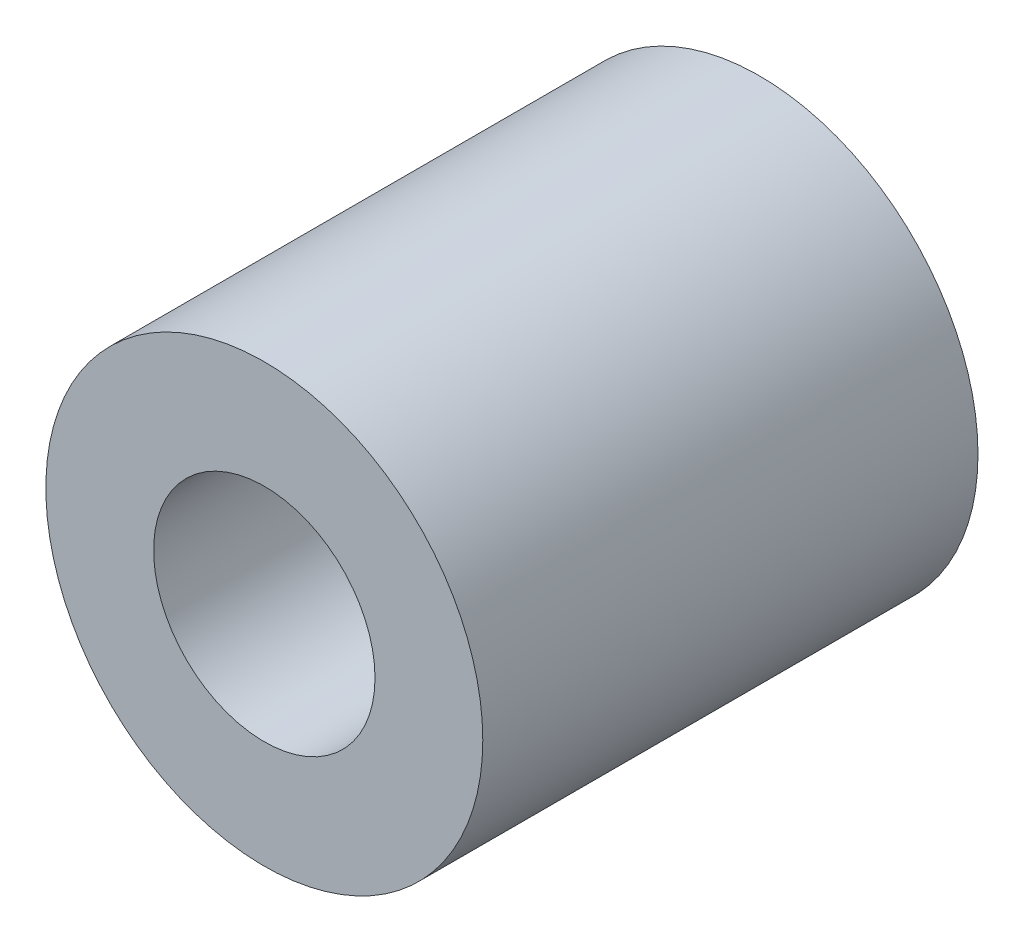
SolidWorks part; units mm, degrees
ref_plane "Front Plane" through (0, 0, 0) normal (0, 0, 1) x (1, 0, 0)
ref_plane "Top Plane" through (0, 0, 0) normal (0, 1, 0) x (1, 0, 0)
ref_plane "Right Plane" through (0, 0, 0) normal (1, 0, 0) x (0, 0, -1)
sketch "Sketch1" plane through (0, 0, 0) normal (0, 0, 1) x (1, 0, 0)
  circle A0 centre (0, 0) radius 4.826
  circle A1 centre (0, 0) radius 9.525
  dimension "D1" = 9.652
  dimension "D2" = 19.05
extrude "Boss-Extrude1" add sketch "Sketch1" along normal blind 21.59
